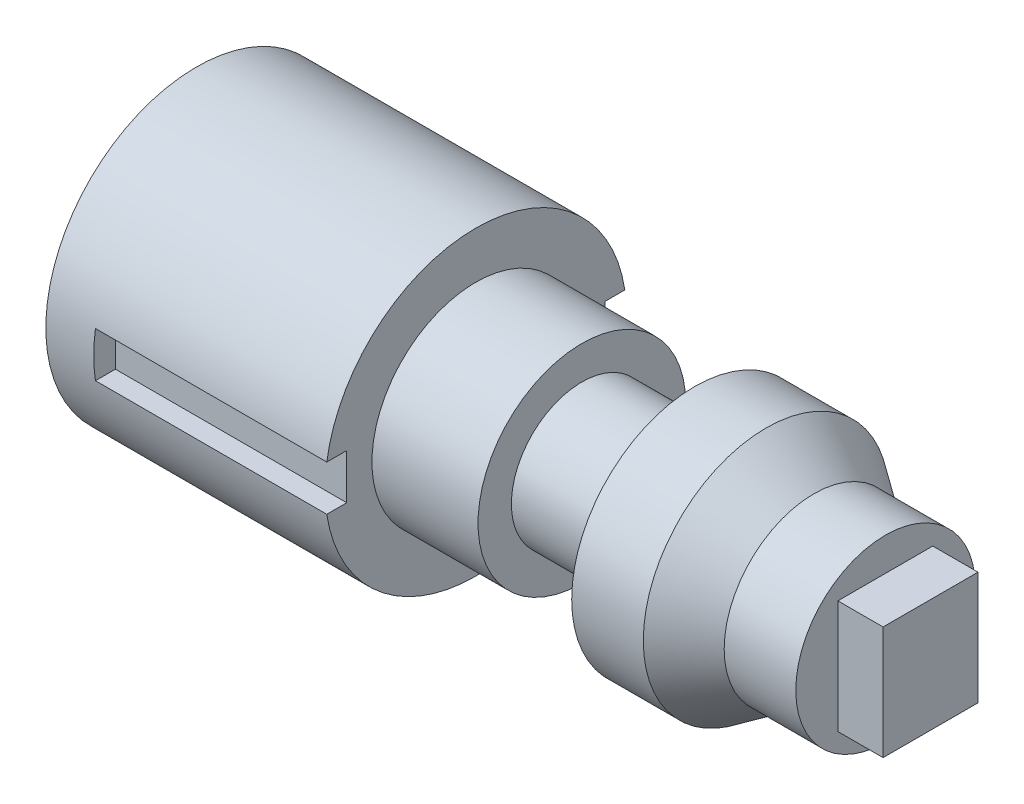
SolidWorks part; units mm, degrees
ref_plane "Front Plane" through (0, 0, 0) normal (0, 0, 1) x (1, 0, 0)
ref_plane "Top Plane" through (0, 0, 0) normal (0, 1, 0) x (1, 0, 0)
ref_plane "Right Plane" through (0, 0, 0) normal (1, 0, 0) x (0, 0, -1)
sketch "Sketch1" plane through (0, 0, 0) normal (0, 1, 0) x (1, 0, 0)
  line L0 (0, 0) -> (0, 10)
  line L1 (0, 10) -> (18.5257, 10)
  line L2 (18.5257, 10) -> (18.5257, 6.8902)
  line L3 (18.5257, 6.8902) -> (25.5633, 6.8902)
  line L4 (25.5633, 6.8902) -> (25.5633, 4.6775)
  line L5 (25.5633, 4.6775) -> (33.0408, 4.6775)
  line L6 (33.0408, 4.6775) -> (33.0408, 8.1526)
  line L7 (33.0408, 8.1526) -> (37.7912, 8.1526)
  line L8 (37.7912, 8.1526) -> (40.9581, 5.9534)
  line L9 (40.9581, 5.9534) -> (45.7085, 5.9534)
  line L10 (45.7085, 5.9534) -> (45.7085, 0)
  line L11 (45.7085, 0) -> (0, 0)
  dimension "D1" = 10
revolve "Revolve1" add sketch "Sketch1" angle 360 about L11
sketch "Sketch2" plane through (0, 0, 0) normal (0, 1, 0) x (1, 0, 0)
  line L0 (0, 0) -> (59.9731, 0) construction
  line L1 (3.1789, 10.7378) -> (21.0656, 10.7378)
  line L2 (3.1789, 10.7378) -> (3.1789, 8.5624)
  line L3 (3.1789, 8.5624) -> (21.0656, 8.5624)
  line L4 (21.0656, 10.7378) -> (21.0656, 8.5624)
  line L5 (21.0656, -10.7378) -> (21.0656, -8.5624)
  line L6 (3.1789, -8.5624) -> (21.0656, -8.5624)
  line L7 (3.1789, -10.7378) -> (3.1789, -8.5624)
  line L8 (3.1789, -10.7378) -> (21.0656, -10.7378)
extrude "Cut-Extrude1" cut sketch "Sketch2" against normal mid plane 3 contours L1 L4 L3 L2 | L6 L5 L8 L7
sketch "Sketch3" plane through (45.7085, 0, 0) normal (1, 0, 0) x (0, 0, -1)
  line L1 (-3.1606, 3.7533) -> (3.1363, 3.7533)
  line L2 (-3.1606, 3.7533) -> (-3.1606, -3.7557)
  line L3 (-3.1606, -3.7557) -> (3.1363, -3.7557)
  line L4 (3.1363, 3.7533) -> (3.1363, -3.7557)
extrude "Boss-Extrude1" add sketch "Sketch3" along normal blind 3
